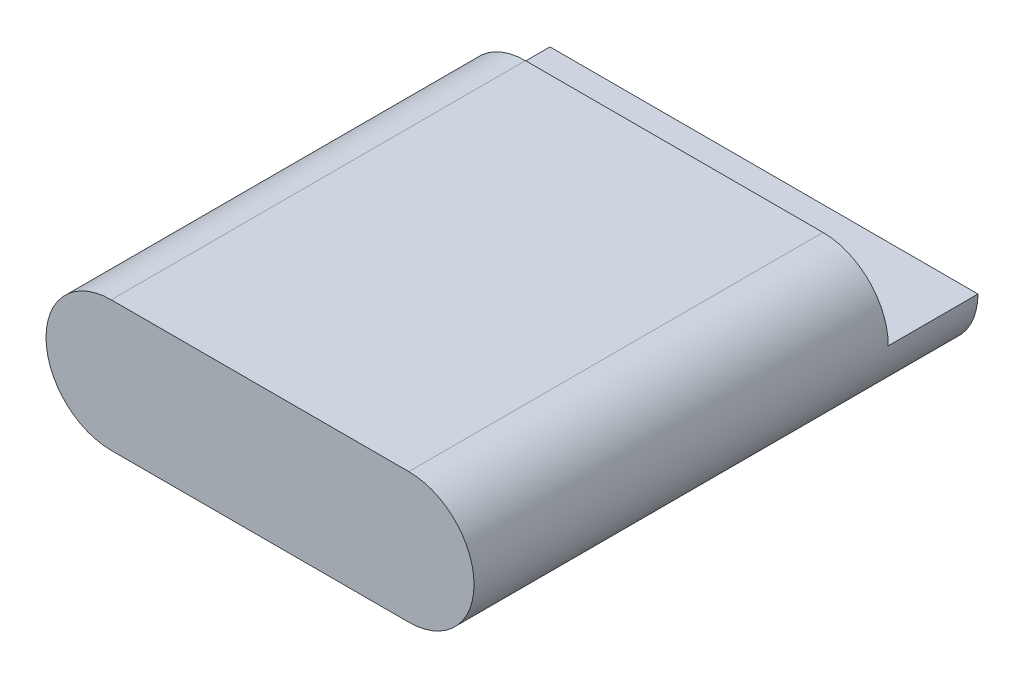
SolidWorks part; units mm, degrees
ref_plane "Front Plane" through (0, 0, 0) normal (0, 0, 1) x (1, 0, 0)
ref_plane "Top Plane" through (0, 0, 0) normal (0, 1, 0) x (1, 0, 0)
ref_plane "Right Plane" through (0, 0, 0) normal (1, 0, 0) x (0, 0, -1)
sketch "Battery Base Sketch" plane through (0, 0, 0) normal (0, 0, 1) x (1, 0, 0)
  line L0 (-10.775, 0) -> (10.775, 0) construction
  line L1 (-10.775, 4.725) -> (10.775, 4.725)
  line L2 (-10.775, -4.725) -> (10.775, -4.725)
  line L3 (-15.5, 0) -> (15.5, 0) construction
  arc A0 (-10.775, 4.725) -> (-10.775, -4.725) centre (-10.775, 0) ccw
  arc A1 (10.775, -4.725) -> (10.775, 4.725) centre (10.775, 0) ccw
  point P3 (0, 0)
  dimension "D2" = 31
  dimension "D1" = 9.45
extrude "Battery Base" add sketch "Battery Base Sketch" along normal blind 36.5
sketch "Pins Sketch" plane through (0, 0, 0) normal (0, 0, -1) x (-1, 0, 0)
  line L0 (-15.4999, -0.025) -> (15.4999, -0.025)
  line L1 (-10.775, 4.725) -> (10.775, 4.725)
  arc A0 (-10.775, 4.725) -> (-15.4999, -0.025) centre (-10.775, 0) ccw
  arc A1 (-10.775, 4.725) -> (-10.775, -4.725) centre (-10.775, 0) ccw construction
  arc A2 (10.775, 4.725) -> (15.4999, -0.025) centre (10.775, 0) cw
  arc A3 (10.775, -4.725) -> (10.775, 4.725) centre (10.775, 0) ccw construction
  dimension "D1" = 4.75
extrude "Pins" cut sketch "Pins Sketch" against normal blind 6.5
ref_plane "Mid Plane" through (0, 0, 18.25) normal (0, 0, 1) x (1, 0, 0)
